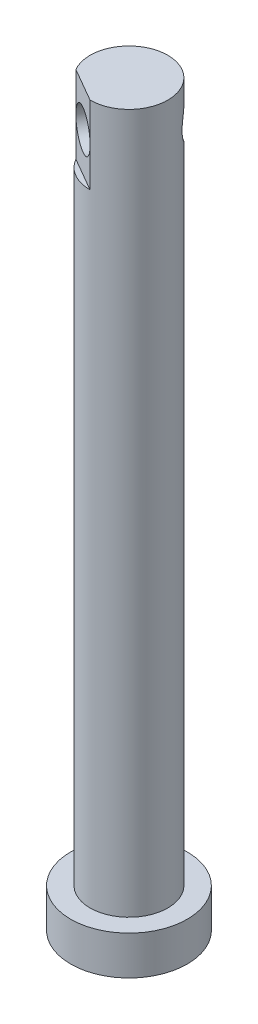
SolidWorks part; units mm, degrees
ref_plane "Спереди" through (0, 0, 0) normal (0, 0, 1) x (1, 0, 0)
ref_plane "Сверху" through (0, 0, 0) normal (0, 1, 0) x (1, 0, 0)
ref_plane "Справа" through (0, 0, 0) normal (1, 0, 0) x (0, 0, -1)
sketch "Эскиз1" plane through (0, 0, 0) normal (0, 1, 0) x (1, 0, 0)
  circle A0 centre (40.8101, -30.2115) radius 7.5
  dimension "D1" = 15
extrude "Бобышка-Вытянуть1" add sketch "Эскиз1" along normal blind 5
sketch "Эскиз2" plane through (0, 5, 0) normal (0, 1, 0) x (1, 0, 0)
  circle A0 centre (40.8101, -30.2115) radius 5
  dimension "D1" = 10
extrude "Бобышка-Вытянуть2" add sketch "Эскиз2" along normal blind 90
sketch "Эскиз12" plane through (0, 95, 0) normal (0, 1, 0) x (1, 0, 0)
  line L0 (40.8101, -35.2115) -> (36.479, -32.7098)
  line L1 (40.8101, -35.2115) -> (40.4709, -35.7988)
  line L2 (36.479, -32.7098) -> (36.1398, -33.297)
  line L3 (40.4709, -35.7988) -> (36.1398, -33.297)
  circle A0 centre (40.8101, -30.2115) radius 5
extrude "Вырез-Вытянуть1" cut sketch "Эскиз12" against normal blind 10 contours L0 L2 L3 L1
sketch "Эскиз13" plane through (-5.0409, 0, 8.727) normal (-0.5002, 0, 0.8659) x (0.8659, 0, 0.5002)
  line L0 (47.9487, 85) -> (47.9487, 95) construction
  line L1 (52.9504, 95) -> (47.9487, 95)
  line L2 (52.9504, 95) -> (52.9504, 90)
  line L3 (52.9504, 90) -> (47.9487, 90)
  line L4 (47.9487, 95) -> (47.9487, 90)
  circle A0 centre (50.4496, 90) radius 2.5009
extrude "Вырез-Вытянуть2" cut sketch "Эскиз13" against normal blind 10 contours A0
